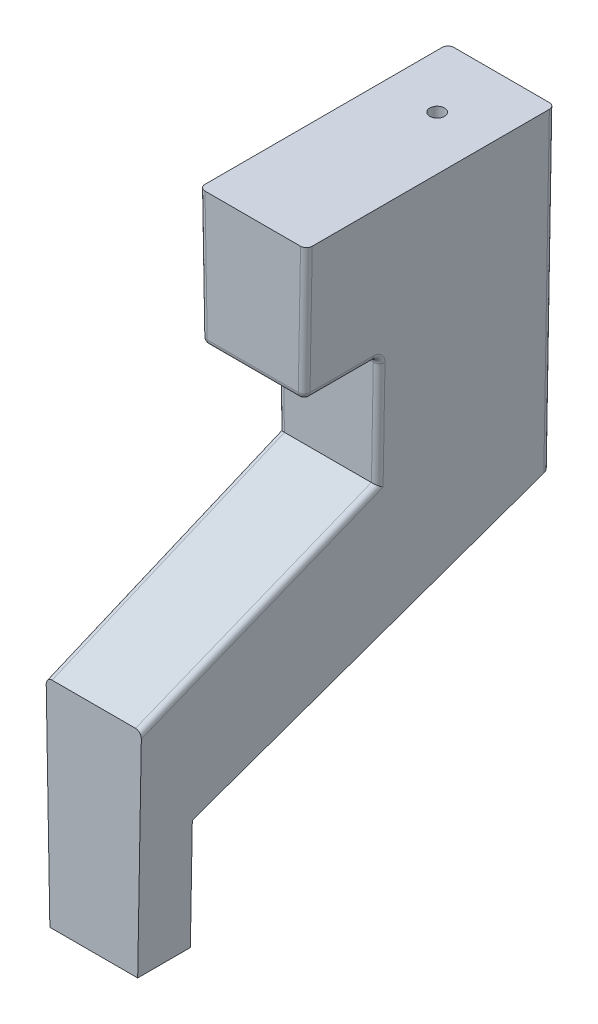
SolidWorks part; units mm, degrees
material "ABS"
ref_plane "Front Plane" through (0, 0, 0) normal (0, 0, 1) x (1, 0, 0)
ref_plane "Top Plane" through (0, 0, 0) normal (0, 1, 0) x (1, 0, 0)
ref_plane "Right Plane" through (0, 0, 0) normal (1, 0, 0) x (0, 0, -1)
sketch "Sketch1" plane through (0, 0, 0) normal (1, 0, 0) x (0, 0, -1)
  line L0 (0.9, 1.9) -> (0.9, 0)
  line L1 (0, 3.675) -> (4, 5.3251)
  line L2 (4, 5.3251) -> (4, 7.2189)
  line L3 (2.7158, 9.5) -> (6.9661, 9.5)
  line L5 (2.7158, 9.5) -> (2.7158, 7.2189)
  line L6 (0, 0) -> (0.9, 0)
  line L7 (0, 0) -> (0, 3.675)
  line L8 (6.9061, -4.2681) -> (6.407, -3.9335) construction
  line L10 (2.7158, 7.2189) -> (4, 7.2189)
  line L14 (0.9, 1.9) -> (6.9661, 4.1079)
  line L15 (6.9661, 4.1079) -> (6.9661, 9.5)
  dimension "D1" = 1.9
  dimension "D2" = 0.9
  dimension "D3" = 4
  dimension "D4" = 20
  dimension "D5" = 9.5
sketch "Sketch4" plane through (0, 0, 0) normal (1, 0, 0) x (0, 0, -1)
  line L0 (12.364, -1.4145) -> (12.364, 2.1305) construction
  line L1 (0, 0) -> (0, 3.675) construction
  dimension "D1" = 12.364
extrude "Boss-Extrude1" add sketch "Sketch1" along normal blind 1.5
draft "Draft4" type of draft neutral plane draft angle 1 neutral plane "Top Plane" faces to draft 2 face at (0, 4.8446, -2.9164) face at (1.5, 4.8446, -2.9164) neutral plane through (0, 0, 0) neutral plane normal (0, 1, 0) reverse direction yes parameters "D1"=1
fillet "Fillet1" radius 0.1 12 edges at (1.626, 7.2189, -3.3579) (1.6459, 8.3595, -2.7158) (0.75, 7.2189, -2.7158) (0.75, 7.2189, -4) (-0.126, 7.2189, -3.3579) (-0.1459, 8.3595, -2.7158) (-0.1188, 6.8039, -6.9661) (1.6188, 6.8039, -6.9661) (1.6095, 6.272, -4) (-0.1095, 6.272, -4) (-0.0785, 4.5001, -2) (1.5785, 4.5001, -2)
sketch "Sketch5" plane through (0, 9.5, 0) normal (0, 1, 0) x (1, 0, 0)
  line L0 (0.75, 6.9661) -> (0.75, -2.6454) construction
  line L1 (1.5658, 6.9661) -> (-0.0658, 6.9661) construction
  circle A0 centre (0.75, 5.8661) radius 0.125
  dimension "D1" = 0.25
  dimension "D2" = 1.1
extrude "Cut-Extrude1" cut sketch "Sketch5" against normal blind 2.5
